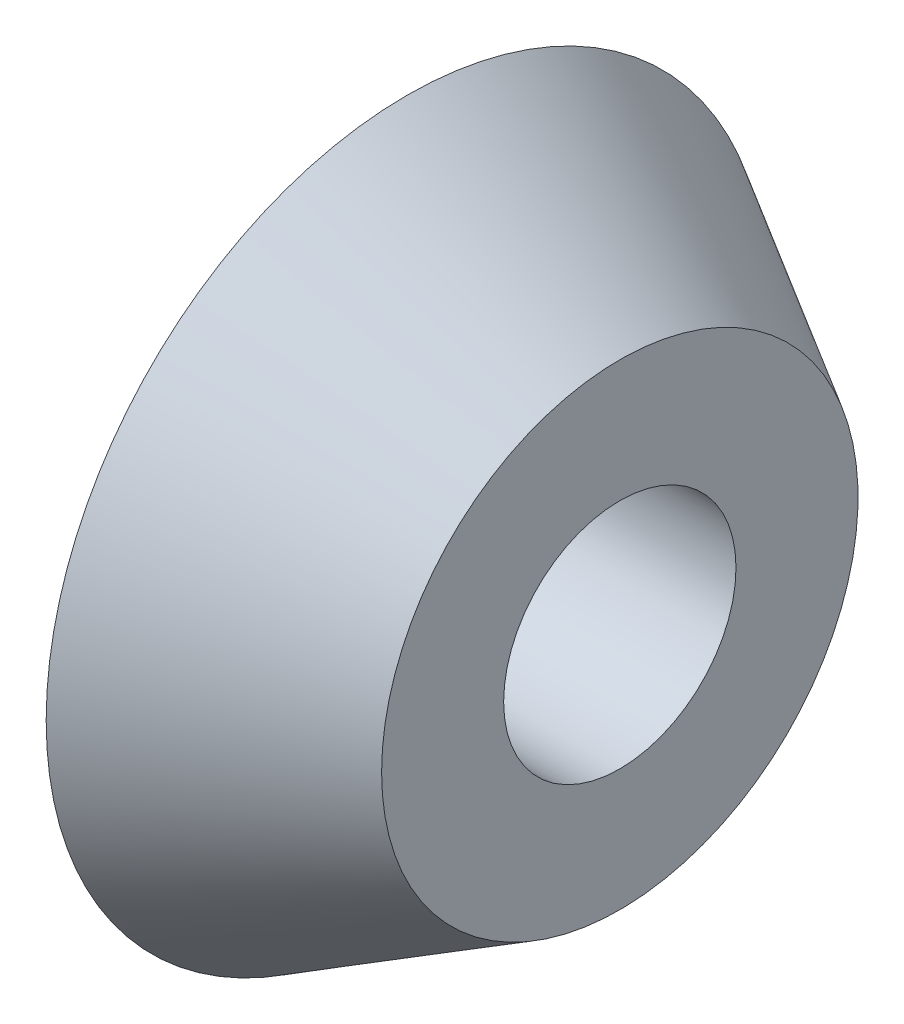
SolidWorks part; units mm, degrees
material "6061-T6 (SS)"
ref_plane "Front Plane" through (0, 0, 0) normal (0, 0, 1) x (1, 0, 0)
ref_plane "Top Plane" through (0, 0, 0) normal (0, 1, 0) x (1, 0, 0)
ref_plane "Right Plane" through (0, 0, 0) normal (1, 0, 0) x (0, 0, -1)
sketch "Sketch1" plane through (0, 0, 0) normal (0, 0, 1) x (1, 0, 0)
  line L0 (0, 0) -> (106.589, 0) construction
  line L1 (4.4132, 8.0518) -> (25.5012, 8.0518)
  line L2 (25.5012, 8.0518) -> (25.5012, 16.51)
  line L3 (25.5012, 16.51) -> (10.7632, 25.019)
  line L4 (10.7632, 25.019) -> (10.7632, 16.51)
  line L5 (9.7472, 15.494) -> (4.4132, 15.494)
  line L6 (4.4132, 15.494) -> (4.4132, 8.0518)
  line L7 (9.7472, 15.494) -> (10.7632, 16.51)
  dimension "D7" = 1.016
  dimension "D6" = 1.016
  dimension "D1" = 30
  dimension "D2" = 8.0518
  dimension "D3" = 16.51
  dimension "D4" = 6.35
  dimension "D5" = 16.51
revolve "Revolve1" add sketch "Sketch1" angle 360 about L0
